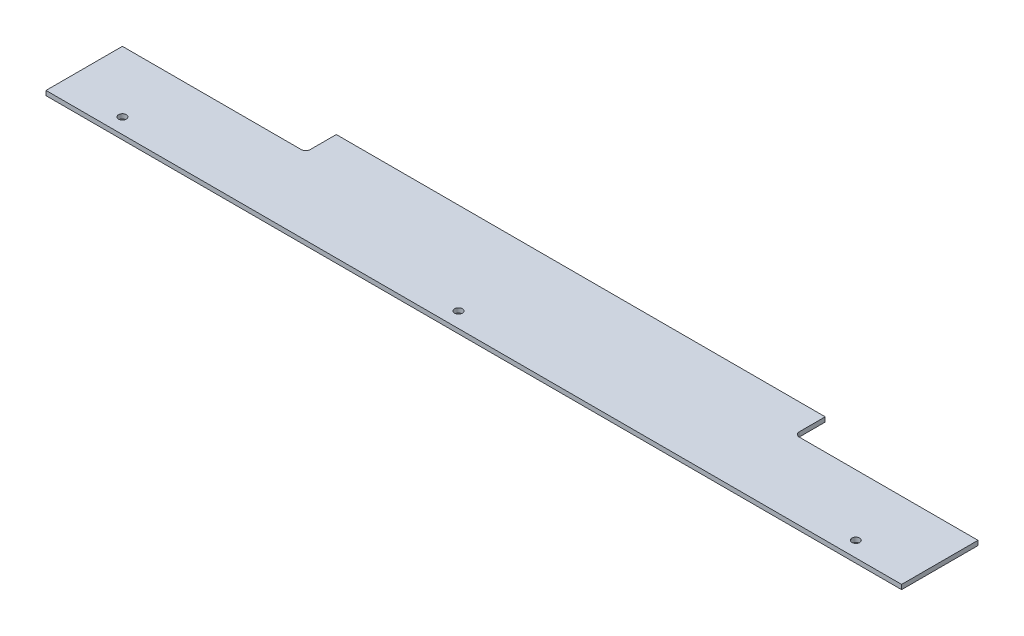
SolidWorks part; units mm, degrees
ref_plane "Front Plane" through (0, 0, 0) normal (0, 0, 1) x (1, 0, 0)
ref_plane "Top Plane" through (0, 0, 0) normal (0, 1, 0) x (1, 0, 0)
ref_plane "Right Plane" through (0, 0, 0) normal (1, 0, 0) x (0, 0, -1)
sketch "Sketch1" plane through (0, 0, 0) normal (0, 1, 0) x (1, 0, 0)
  line L0 (-170, 27.5) -> (-170, 10.5)
  line L1 (-170, 27.5) -> (150, 27.5)
  line L3 (-290, -42.5) -> (270, -42.5)
  line L7 (-173, 7.5) -> (-290, 7.5)
  line L8 (-290, 7.5) -> (-290, -42.5)
  line L9 (150, 27.5) -> (150, 10.5)
  line L10 (153, 7.5) -> (270, 7.5)
  line L11 (270, 7.5) -> (270, -42.5)
  arc A0 (-173, 7.5) -> (-170, 10.5) centre (-173, 10.5) ccw
  arc A1 (150, 10.5) -> (153, 7.5) centre (153, 10.5) ccw
  circle A2 centre (-250, -32.5) radius 2.55
  circle A3 centre (-30, -32.5) radius 2.55
  circle A4 centre (230, -32.5) radius 2.55
  point P0 (0, 0)
  point P3 (-170, 7.5)
  dimension "D5" = 3
  dimension "D6" = 10
  dimension "D7" = 5.1
  dimension "D8" = 40
  dimension "D9" = 40
  dimension "D10" = 300
  dimension "D1" = 70
  dimension "D2" = 560
  dimension "D3" = 20
  dimension "D4" = 120
extrude "Boss-Extrude1" add sketch "Sketch1" along normal blind 3
